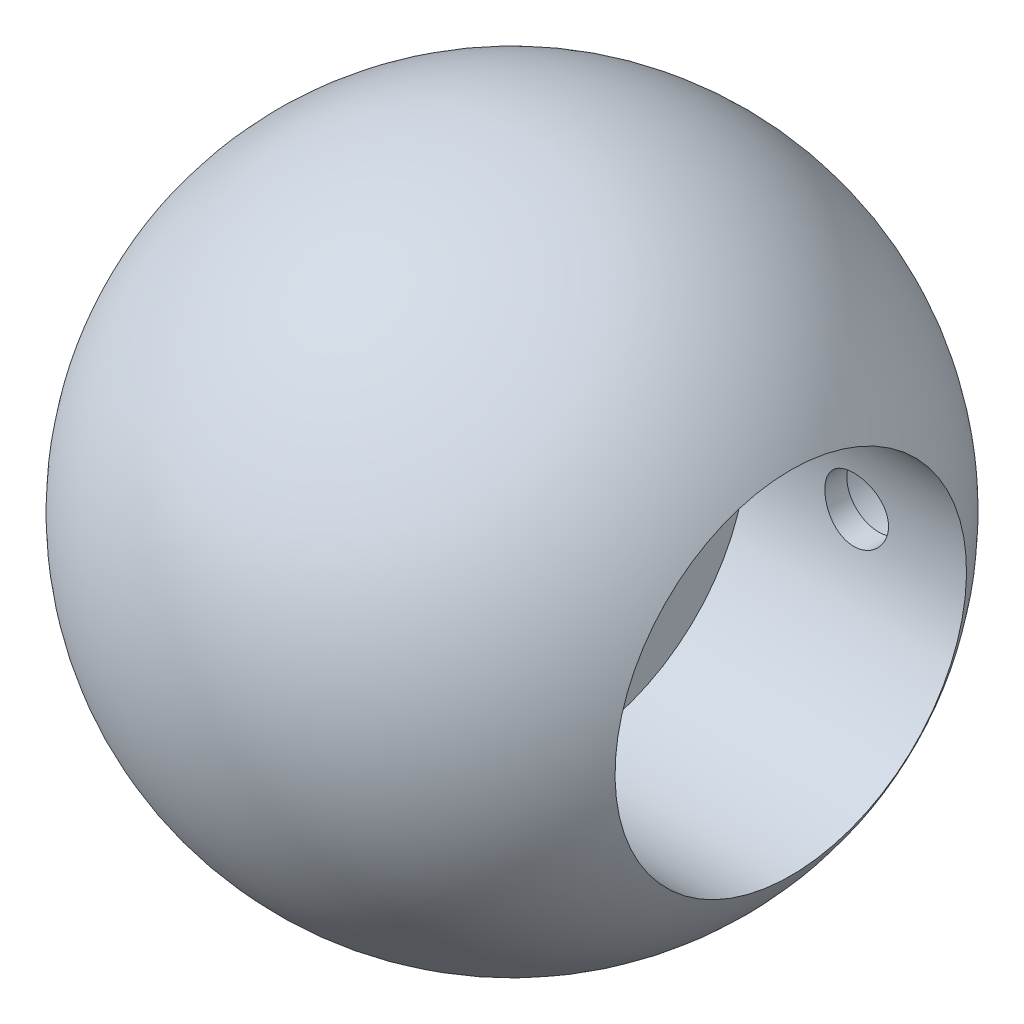
SolidWorks part; units mm, degrees
ref_plane "前视基准面" through (0, 0, 0) normal (0, 0, 1) x (1, 0, 0)
ref_plane "上视基准面" through (0, 0, 0) normal (0, 1, 0) x (1, 0, 0)
ref_plane "右视基准面" through (0, 0, 0) normal (1, 0, 0) x (0, 0, -1)
sketch "草图1" plane through (0, 0, 0) normal (0, 0, 1) x (1, 0, 0)
  line L0 (0, 0) -> (12.6886, 0) construction
  line L2 (-15, 0) -> (12.6886, 0) construction
  line L3 (12.6886, 8) -> (12.6886, 0)
  line L4 (12.6886, 0) -> (-15, 0)
  arc A0 (12.6886, 8) -> (-15, 0) centre (0, 0) ccw
  dimension "D1" = 8
  dimension "D2" = 30
revolve "旋转8" add sketch "草图1" angle 360 about L4
sketch "草图2" plane through (12.6886, 0, 0) normal (1, 0, 0) x (0, 0, -1)
  circle A0 centre (0, 0) radius 8
extrude "切除-拉伸1" cut sketch "草图2" against normal blind 10
sketch "草图3" plane through (0, 0, 0) normal (0, 0, 1) x (1, 0, 0)
  line L0 (2.6886, -8) -> (2.6886, 8) construction
  circle A0 centre (7.6886, 0) radius 1.45
  dimension "D1" = 2.9
  dimension "D2" = 5
extrude "切除-拉伸4" cut sketch "草图3" against normal blind 9 and the other way blind 11
sketch "草图5" plane through (0, 0, -9) normal (0, 0, 1) x (1, 0, 0)
  circle A0 centre (7.6886, 0) radius 2.55
extrude "切除-拉伸5" cut sketch "草图5" against normal up to next
